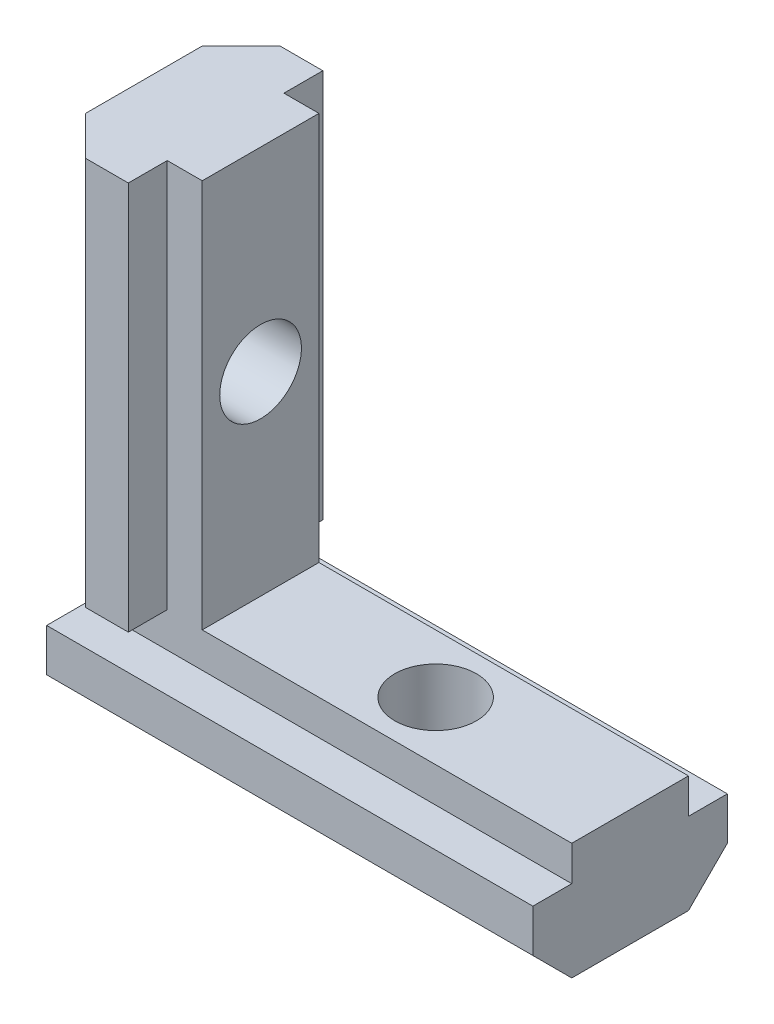
SolidWorks part; units mm, degrees
ref_plane "前视基准面" through (0, 0, 0) normal (0, 0, 1) x (1, 0, 0)
ref_plane "上视基准面" through (0, 0, 0) normal (0, 1, 0) x (1, 0, 0)
ref_plane "右视基准面" through (0, 0, 0) normal (1, 0, 0) x (0, 0, -1)
sketch "草图1" plane through (0, 0, 0) normal (0, 1, 0) x (1, 0, 0)
  line L0 (-3, 0) -> (3, 0) construction
  line L1 (3, -5) -> (-3, -5) construction
  line L2 (3, -5) -> (3, 5) construction
  line L3 (3, 5) -> (-3, 5) construction
  line L4 (-3, -5) -> (-3, 5) construction
  line L5 (3, -5) -> (-3, 5) construction
  line L6 (3, 5) -> (-3, -5) construction
  line L7 (0, -5) -> (0, 5) construction
  line L8 (-3, 3) -> (-3, -3)
  line L9 (-3, -3) -> (-1, -5)
  line L10 (-1, -5) -> (1.2, -5)
  line L11 (1.2, -5) -> (1.2, -3)
  line L12 (1.2, -3) -> (3, -3)
  line L13 (3, -3) -> (3, 3)
  line L14 (1.2, 3) -> (3, 3)
  line L15 (1.2, 5) -> (1.2, 3)
  line L16 (-1, 5) -> (1.2, 5)
  line L17 (-3, 3) -> (-1, 5)
  point P0 (0, 0)
  dimension "D1" = 10
  dimension "D2" = 6
  dimension "D3" = 3
  dimension "D4" = 45
  dimension "D5" = 1.8
  dimension "D6" = 3
extrude "凸台-拉伸1" add sketch "草图1" along normal blind 20
sketch "草图3" plane through (-3, 0, 0) normal (-1, 0, 0) x (0, 0, 1)
  line L0 (0, -6) -> (0, 0) construction
  line L1 (5, 0) -> (5, -6) construction
  line L2 (5, 0) -> (-5, 0) construction
  line L3 (-5, 0) -> (-5, -6) construction
  line L4 (5, -6) -> (-5, -6) construction
  line L5 (5, 0) -> (-5, -6) construction
  line L6 (-5, 0) -> (5, -6) construction
  line L7 (5, -3) -> (-5, -3) construction
  line L8 (-3, -6) -> (3, -6)
  line L9 (3, -6) -> (5, -4)
  line L10 (5, -4) -> (5, -1.8)
  line L11 (5, -1.8) -> (3, -1.8)
  line L12 (3, -1.8) -> (3, 0)
  line L13 (3, 0) -> (-3, 0)
  line L14 (-3, -1.8) -> (-3, 0)
  line L15 (-5, -1.8) -> (-3, -1.8)
  line L16 (-5, -4) -> (-5, -1.8)
  line L17 (-3, -6) -> (-5, -4)
  line L18 (-3, 0) -> (3, 0) construction
  line L19 (-3, 20) -> (-3, 0) construction
  point P0 (0, -3)
  dimension "D1" = 3
  dimension "D2" = 45
  dimension "D3" = 1.8
  dimension "D4" = 3
  dimension "D5" = 10
  dimension "D6" = 6
  dimension "D7" = 10
  dimension "D8" = 0
  dimension "D9" = 0
extrude "凸台-拉伸2" add sketch "草图3" against normal blind 25
sketch "草图4" plane through (-3, 0, 0) normal (-1, 0, 0) x (0, 0, 1)
  line L0 (-3, 20) -> (3, 20) construction
  circle A0 centre (0, 10) radius 2.5
  dimension "D1" = 5
  dimension "D2" = 10
sketch "草图5" plane through (0, -6, 0) normal (0, -1, 0) x (-1, 0, 0)
  line L0 (-22, 3) -> (-22, -3) construction
  circle A0 centre (-12, 0) radius 2.5
  dimension "D1" = 10
  dimension "D2" = 5
hole_wizard "M5 螺纹孔1" positions "草图8" profile "草图9" tap size "M5" standard "GB" end condition through all
sketch "草图8" plane through (-3, 0, 0) normal (-1, 0, 0) x (0, 0, 1)
  point P0 (0, 10)
sketch "草图9" plane through (-3, 10, 0) normal (0, 1, 0) x (0, 0, 1)
  line L0 (0, 0) -> (0, 25)
  line L1 (0, 25) -> (2.1, 25)
  line L2 (2.1, 25) -> (2.1, 0)
  line L5 (2.1, 0) -> (0, 0)
  line L11 (0, -6.35) -> (0, 107.95) construction
  dimension "通孔螺纹孔钻头直径" = 4.2
  dimension "通孔螺纹孔钻头深度" = 25
cosmetic thread "孔螺蚊线1" parameters "D2"=5
hole_wizard "M5 螺纹孔2" positions "草图10" profile "草图11" tap size "M5" standard "GB" end condition through all
sketch "草图10" plane through (0, -6, 0) normal (0, -1, 0) x (-1, 0, 0)
  point P0 (-12, 0)
sketch "草图11" plane through (12, -6, 0) normal (1, 0, 0) x (0, 0, -1)
  line L0 (0, 0) -> (0, 26)
  line L1 (0, 26) -> (2.1, 26)
  line L2 (2.1, 26) -> (2.1, 0)
  line L5 (2.1, 0) -> (0, 0)
  line L11 (0, -6.35) -> (0, 107.95) construction
  dimension "通孔螺纹孔钻头直径" = 4.2
  dimension "通孔螺纹孔钻头深度" = 26
cosmetic thread "孔螺蚊线2" parameters "D2"=5
